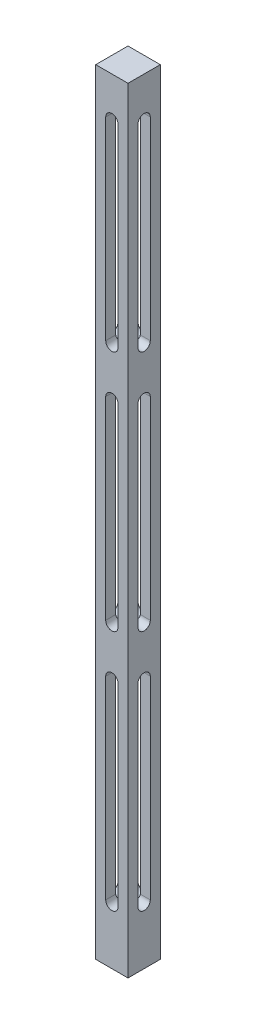
SolidWorks part; units mm, degrees
material "6061-T6 (SS)"
ref_plane "Front Plane" through (0, 0, 0) normal (0, 0, 1) x (1, 0, 0)
ref_plane "Top Plane" through (0, 0, 0) normal (0, 1, 0) x (1, 0, 0)
ref_plane "Right Plane" through (0, 0, 0) normal (1, 0, 0) x (0, 0, -1)
sketch "Sketch1" plane through (0, 0, 0) normal (0, 1, 0) x (1, 0, 0)
  line L1 (-6.35, -6.35) -> (6.35, -6.35)
  line L2 (-6.35, -6.35) -> (-6.35, 6.35)
  line L3 (-6.35, 6.35) -> (6.35, 6.35)
  line L4 (6.35, -6.35) -> (6.35, 6.35)
  line L5 (-6.35, -6.35) -> (6.35, 6.35) construction
  line L6 (-6.35, 6.35) -> (6.35, -6.35) construction
  point P0 (0, 0)
  dimension "D1" = 12.7
  dimension "D2" = 12.7
extrude "Boss-Extrude1" add sketch "Sketch1" along normal blind 304.8
sketch "Sketch2" plane through (0, 0, -6.35) normal (0, 0, -1) x (-1, 0, 0)
  line L0 (-6.35, 304.8) -> (6.35, 304.8) construction
  line L1 (-2.413, 288.925) -> (-2.413, 212.725)
  line L2 (2.413, 288.925) -> (2.413, 212.725)
  arc A0 (2.413, 288.925) -> (-2.413, 288.925) centre (0, 288.925) ccw
  arc A2 (-2.413, 212.725) -> (2.413, 212.725) centre (0, 212.725) ccw
  dimension "D1" = 15.875
  dimension "D2" = 2.413
  dimension "D3" = 76.2
extrude "Cut-Extrude1" cut sketch "Sketch2" against normal through all
sketch "Sketch3" plane through (6.35, 0, 0) normal (1, 0, 0) x (0, 0, -1)
  line L0 (-2.413, 288.925) -> (-2.413, 212.725)
  line L1 (2.413, 288.925) -> (2.413, 212.725)
  line L2 (-6.35, 304.8) -> (6.35, 304.8) construction
  line L3 (6.35, 304.8) -> (6.35, 0) construction
  arc A0 (2.413, 288.925) -> (-2.413, 288.925) centre (0, 288.925) ccw
  arc A1 (-2.413, 212.725) -> (2.413, 212.725) centre (0, 212.725) ccw
  dimension "D4" = 2.413
  dimension "D1" = 15.875
  dimension "D2" = 76.2
  dimension "D3" = 6.35
extrude "Cut-Extrude2" cut sketch "Sketch3" against normal through all
pattern_linear "LPattern1" count 3 spacing 95.25 along (0, -1, 0) of "Cut-Extrude1", "Cut-Extrude2"
